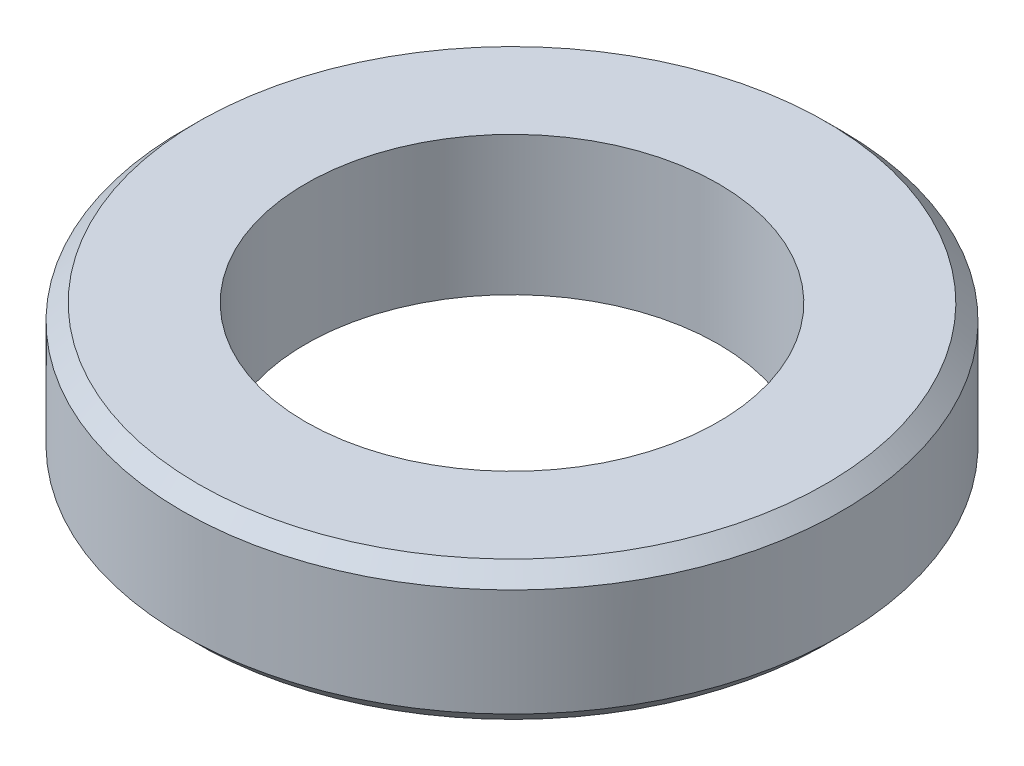
SolidWorks part; units mm, degrees
material "Nylon 101"
ref_plane "Front Plane" through (0, 0, 0) normal (0, 0, 1) x (1, 0, 0)
ref_plane "Top Plane" through (0, 0, 0) normal (0, 1, 0) x (1, 0, 0)
ref_plane "Right Plane" through (0, 0, 0) normal (1, 0, 0) x (0, 0, -1)
sketch "Sketch1" plane through (0, 0, 0) normal (0, 0, 1) x (1, 0, 0)
  line L0 (10.668, 0) -> (6.6802, 0)
  line L1 (6.6802, 0) -> (6.6802, -4.4958)
  line L2 (6.6802, -4.4958) -> (10.668, -4.4958)
  line L4 (10.668, -4.4958) -> (10.668, 0)
  line L6 (0, 0) -> (0, -4.4958) construction
  dimension "D1" = 6.6802
  dimension "D2" = 4.4958
  dimension "D3" = 10.668
revolve "Revolve1" add sketch "Sketch1" angle 360 about L6
chamfer "Chamfer1" distance 0.508 angle 45 2 edges at (0, -4.4958, -10.668) (0, 0, -10.668)
